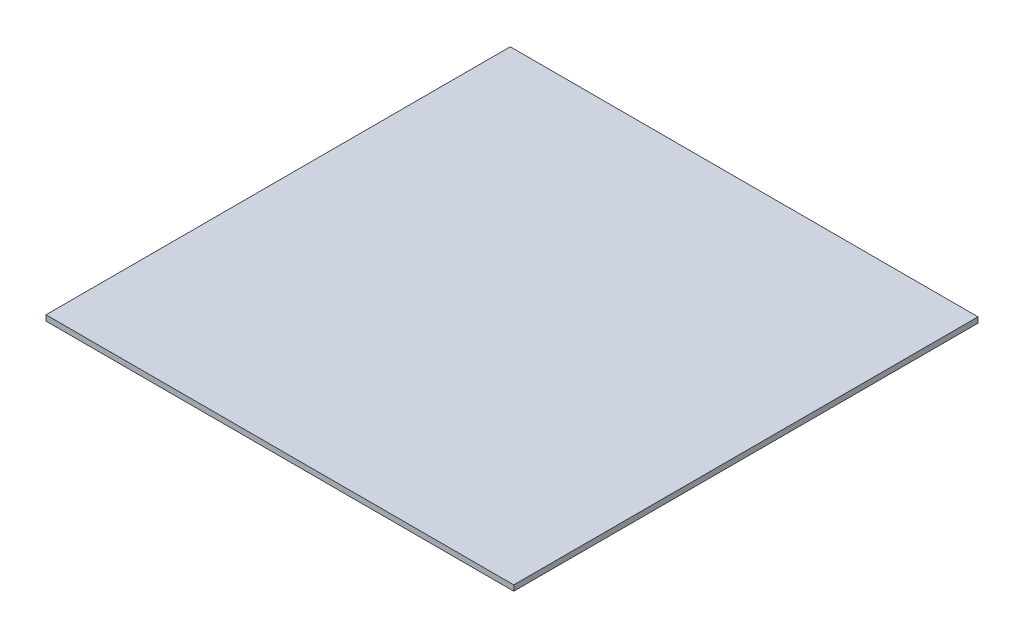
SolidWorks part; units mm, degrees
ref_plane "Front Plane" through (0, 0, 0) normal (0, 0, 1) x (1, 0, 0)
ref_plane "Top Plane" through (0, 0, 0) normal (0, 1, 0) x (1, 0, 0)
ref_plane "Right Plane" through (0, 0, 0) normal (1, 0, 0) x (0, 0, -1)
sketch "Sketch1" plane through (0, 0, 0) normal (0, 1, 0) x (1, 0, 0)
  line L1 (0, 0) -> (134.366, 0)
  line L2 (0, 0) -> (0, 133.35)
  line L3 (0, 133.35) -> (134.366, 133.35)
  line L4 (134.366, 0) -> (134.366, 133.35)
  dimension "D1" = 133.35
  dimension "D2" = 134.366
extrude "Boss-Extrude1" add sketch "Sketch1" along normal blind 1.5875
